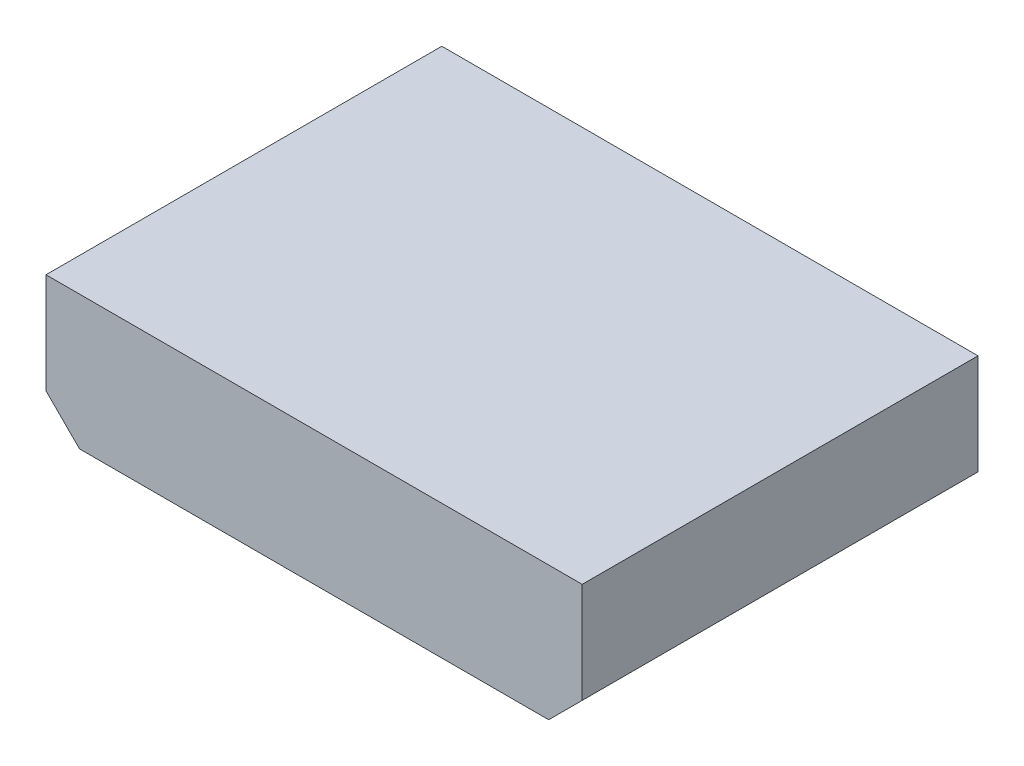
SolidWorks part; units mm, degrees
ref_plane "Front Plane" through (0, 0, 0) normal (0, 0, 1) x (1, 0, 0)
ref_plane "Top Plane" through (0, 0, 0) normal (0, 1, 0) x (1, 0, 0)
ref_plane "Right Plane" through (0, 0, 0) normal (1, 0, 0) x (0, 0, -1)
sketch "Sketch1" plane through (0, 0, 0) normal (0, 0, 1) x (1, 0, 0)
  line L0 (-5.08, 2.54) -> (-5.08, -1.27)
  line L1 (-5.08, -1.27) -> (-3.81, -2.54)
  line L2 (-3.81, -2.54) -> (13.97, -2.54)
  line L3 (13.97, -2.54) -> (15.24, -1.27)
  line L4 (15.24, -1.27) -> (15.24, 2.54)
  line L5 (15.24, 2.54) -> (-5.08, 2.54)
extrude "Component_Outline" add sketch "Sketch1" along normal blind 15 separate body
sketch "Sketch2" plane through (0, 0, 0) normal (0, 0, 1) x (1, 0, 0)
  circle A0 centre (0, 0) radius 0.25
extrude "1" add sketch "Sketch2" against normal blind 2 separate body
sketch "Sketch3" plane through (0, 0, 0) normal (0, 0, 1) x (1, 0, 0)
  circle A0 centre (2.54, 0) radius 0.25
extrude "2" add sketch "Sketch3" against normal blind 2 separate body
sketch "Sketch4" plane through (0, 0, 0) normal (0, 0, 1) x (1, 0, 0)
  circle A0 centre (5.08, 0) radius 0.25
extrude "3" add sketch "Sketch4" against normal blind 2 separate body
sketch "Sketch5" plane through (0, 0, 0) normal (0, 0, 1) x (1, 0, 0)
  circle A0 centre (7.62, 0) radius 0.25
extrude "4" add sketch "Sketch5" against normal blind 2 separate body
sketch "Sketch6" plane through (0, 0, 0) normal (0, 0, 1) x (1, 0, 0)
  circle A0 centre (10.16, 0) radius 0.25
extrude "5" add sketch "Sketch6" against normal blind 2 separate body
sketch3d "3DSketch1"
  line L0 (0, 0, 0) -> (1, 0, 0)
  line L1 (0, 0, 0) -> (0, 1, 0)
  line L2 (0, 0, 0) -> (0, 0, 1)
  point P0 (0, 0, 0)
